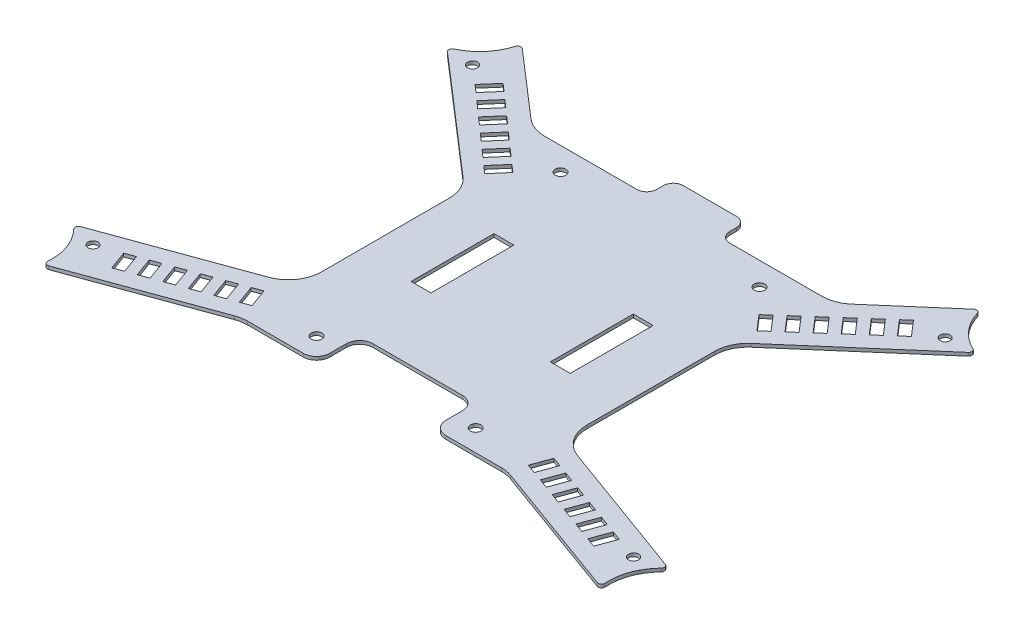
SolidWorks part; units mm, degrees
material "Thornel Mat VMA"
ref_plane "Front Plane" through (0, 0, 0) normal (0, 0, 1) x (1, 0, 0)
ref_plane "Top Plane" through (0, 0, 0) normal (0, 1, 0) x (1, 0, 0)
ref_plane "Right Plane" through (0, 0, 0) normal (1, 0, 0) x (0, 0, -1)
sketch "Sketch2" plane through (0, 0, 0) normal (0, 1, 0) x (1, 0, 0)
  line L24 (11, 53) -> (11, 55)
  line L25 (8, 58) -> (-8, 58)
  line L26 (-11, 55) -> (-11, 53)
  line L27 (-14, 50) -> (-41.7933, 50)
  line L28 (-48.3393, 52.4403) -> (-69.5576, 70.8135)
  line L29 (-80.0313, 58.718) -> (-43.4539, 27.0451)
  line L30 (-40, 19.4854) -> (-40, -19.0433)
  line L31 (-46.5798, -28.4402) -> (-90.0503, -44.2622)
  line L32 (-84.578, -59.2973) -> (-41.6569, -43.6753)
  line L33 (-38.2367, -43.0722) -> (-21.5, -43.0722)
  line L34 (-17.5, -39.0722) -> (-17.5, -34.0722)
  line L35 (-13.5, -30.0722) -> (13.5, -30.0722)
  line L36 (17.5, -34.0722) -> (17.5, -39.0722)
  line L37 (21.5, -43.0722) -> (38.2367, -43.0722)
  line L38 (41.6569, -43.6753) -> (84.578, -59.2973)
  line L39 (90.0503, -44.2622) -> (46.5798, -28.4402)
  line L40 (40, -19.0433) -> (40, 19.4854)
  line L41 (43.4539, 27.0451) -> (80.0313, 58.718)
  line L42 (69.5576, 70.8135) -> (48.3393, 52.4403)
  line L43 (41.7933, 50) -> (14, 50)
  line L88 (-48.3393, 52.4403) -> (-68.0517, 69.5096)
  line L89 (-78.5254, 57.4141) -> (-43.4539, 27.0451)
  line L90 (-40, 19.4854) -> (-40, -19.0433)
  line L91 (-46.5798, -28.4402) -> (-88.1785, -43.5809)
  line L92 (-82.7062, -58.616) -> (-41.6569, -43.6753)
  line L93 (-38.2367, -43.0722) -> (-21.5, -43.0722)
  line L94 (-17.5, -39.0722) -> (-17.5, -34.0722)
  line L95 (-13.5, -30.0722) -> (13.5, -30.0722)
  line L96 (17.5, -34.0722) -> (17.5, -39.0722)
  line L97 (21.5, -43.0722) -> (38.2367, -43.0722)
  line L98 (41.6569, -43.6753) -> (82.7062, -58.616)
  line L99 (88.1785, -43.5809) -> (46.5798, -28.4402)
  line L100 (40, -19.0433) -> (40, 19.4854)
  line L101 (43.4539, 27.0451) -> (78.5254, 57.4141)
  line L102 (68.0517, 69.5096) -> (48.3393, 52.4403)
  line L103 (41.7933, 50) -> (14, 50)
  line L104 (11, 53) -> (11, 55)
  line L105 (8, 58) -> (-8, 58)
  line L106 (11, 53) -> (11, 55)
  line L107 (-14, 50) -> (-41.7933, 50)
  line L108 (-48.3393, 52.4403) -> (-68.0517, 69.5096)
  line L109 (-78.5254, 57.4141) -> (-43.4539, 27.0451)
  line L110 (-40, 19.4854) -> (-40, -19.0433)
  line L111 (-46.5798, -28.4402) -> (-88.1785, -43.5809)
  line L112 (-82.7062, -58.616) -> (-41.6569, -43.6753)
  line L113 (-38.2367, -43.0722) -> (-21.5, -43.0722)
  line L114 (-17.5, -39.0722) -> (-17.5, -34.0722)
  line L115 (-13.5, -30.0722) -> (13.5, -30.0722)
  line L116 (17.5, -34.0722) -> (17.5, -39.0722)
  line L117 (21.5, -43.0722) -> (38.2367, -43.0722)
  line L118 (41.6569, -43.6753) -> (82.7062, -58.616)
  line L119 (88.1785, -43.5809) -> (46.5798, -28.4402)
  line L120 (40, -19.0433) -> (40, 19.4854)
  line L121 (43.4539, 27.0451) -> (78.5254, 57.4141)
  line L122 (68.0517, 69.5096) -> (48.3393, 52.4403)
  line L123 (41.7933, 50) -> (14, 50)
  line L125 (8, 58) -> (-8, 58)
  line L127 (-14, 50) -> (-41.7933, 50)
  line L180 (-11, 55) -> (-11, 53)
  line L181 (-11, 55) -> (-11, 53)
  arc A28 (11, 55) -> (8, 58) centre (8, 55) ccw
  arc A29 (-8, 58) -> (-11, 55) centre (-8, 55) ccw
  arc A30 (-14, 50) -> (-11, 53) centre (-14, 53) ccw
  arc A31 (-48.3393, 52.4403) -> (-41.7933, 50) centre (-41.7933, 60) ccw
  arc A32 (-72.7842, 76.2531) -> (-69.5576, 70.8135) centre (-63.0115, 78.3732) ccw
  arc A33 (-72.7842, 76.2531) -> (-85.8763, 61.1337) centre (-85, 73.603) ccw
  arc A34 (-80.0313, 58.718) -> (-85.8763, 61.1337) centre (-86.5773, 51.1583) ccw
  arc A35 (-40, 19.4854) -> (-43.4539, 27.0451) centre (-50, 19.4854) ccw
  arc A36 (-46.5798, -28.4402) -> (-40, -19.0433) centre (-50, -19.0433) ccw
  arc A37 (-96.3725, -44.4349) -> (-90.0503, -44.2622) centre (-93.4705, -34.8653) ccw
  arc A38 (-96.3725, -44.4349) -> (-89.5321, -63.2288) centre (-100, -56.397) ccw
  arc A39 (-84.578, -59.2973) -> (-89.5321, -63.2288) centre (-81.1578, -68.6942) ccw
  arc A40 (-38.2367, -43.0722) -> (-41.6569, -43.6753) centre (-38.2367, -53.0722) ccw
  arc A41 (-21.5, -43.0722) -> (-17.5, -39.0722) centre (-21.5, -39.0722) ccw
  arc A42 (-13.5, -30.0722) -> (-17.5, -34.0722) centre (-13.5, -34.0722) ccw
  arc A43 (17.5, -34.0722) -> (13.5, -30.0722) centre (13.5, -34.0722) ccw
  arc A44 (17.5, -39.0722) -> (21.5, -43.0722) centre (21.5, -39.0722) ccw
  arc A45 (41.6569, -43.6753) -> (38.2367, -43.0722) centre (38.2367, -53.0722) ccw
  arc A46 (89.5321, -63.2288) -> (84.578, -59.2973) centre (81.1578, -68.6942) ccw
  arc A47 (89.5321, -63.2288) -> (96.3725, -44.4349) centre (100, -56.397) ccw
  arc A48 (90.0503, -44.2622) -> (96.3725, -44.4349) centre (93.4705, -34.8653) ccw
  arc A49 (40, -19.0433) -> (46.5798, -28.4402) centre (50, -19.0433) ccw
  arc A50 (43.4539, 27.0451) -> (40, 19.4854) centre (50, 19.4854) ccw
  arc A51 (85.8763, 61.1337) -> (80.0313, 58.718) centre (86.5773, 51.1583) ccw
  arc A52 (85.8763, 61.1337) -> (72.7842, 76.2531) centre (85, 73.603) ccw
  arc A53 (69.5576, 70.8135) -> (72.7842, 76.2531) centre (63.0115, 78.3732) ccw
  arc A54 (41.7933, 50) -> (48.3393, 52.4403) centre (41.7933, 60) ccw
  arc A55 (11, 53) -> (14, 50) centre (14, 53) ccw
  arc A61 (-72.7842, 76.2531) -> (-85.8763, 61.1337) centre (-85, 73.603) ccw construction
  arc A80 (85.8763, 61.1337) -> (72.7842, 76.2531) centre (85, 73.603) ccw construction
  arc A81 (69.5576, 70.8135) -> (72.7842, 76.2531) centre (63.0115, 78.3732) ccw construction
  arc A113 (-78.2902, 59.0779) -> (-69.6648, 69.0389) centre (-85, 73.603) ccw
  arc A115 (-40, 19.4854) -> (-43.4539, 27.0451) centre (-50, 19.4854) ccw
  arc A116 (-46.5798, -28.4402) -> (-40, -19.0433) centre (-50, -19.0433) ccw
  arc A118 (-84.0454, -57.6011) -> (-88.552, -45.2192) centre (-100, -56.397) ccw
  arc A120 (-38.2367, -43.0722) -> (-41.6569, -43.6753) centre (-38.2367, -53.0722) ccw
  arc A121 (-21.5, -43.0722) -> (-17.5, -39.0722) centre (-21.5, -39.0722) ccw
  arc A122 (-13.5, -30.0722) -> (-17.5, -34.0722) centre (-13.5, -34.0722) ccw
  arc A123 (17.5, -34.0722) -> (13.5, -30.0722) centre (13.5, -34.0722) ccw
  arc A124 (17.5, -39.0722) -> (21.5, -43.0722) centre (21.5, -39.0722) ccw
  arc A125 (41.6569, -43.6753) -> (38.2367, -43.0722) centre (38.2367, -53.0722) ccw
  arc A127 (88.552, -45.2192) -> (84.0454, -57.6011) centre (100, -56.397) ccw
  arc A129 (40, -19.0433) -> (46.5798, -28.4402) centre (50, -19.0433) ccw
  arc A130 (43.4539, 27.0451) -> (40, 19.4854) centre (50, 19.4854) ccw
  arc A132 (69.6648, 69.0389) -> (78.2902, 59.0779) centre (85, 73.603) ccw
  arc A134 (41.7933, 50) -> (48.3393, 52.4403) centre (41.7933, 60) ccw
  arc A135 (11, 53) -> (14, 50) centre (14, 53) ccw
  arc A136 (11, 55) -> (8, 58) centre (8, 55) ccw
  arc A137 (-8, 58) -> (-11, 55) centre (-8, 55) ccw
  arc A138 (-14, 50) -> (-11, 53) centre (-14, 53) ccw
  arc A139 (-48.3393, 52.4403) -> (-41.7933, 50) centre (-41.7933, 60) ccw
  arc A141 (-78.2902, 59.0779) -> (-69.6648, 69.0389) centre (-85, 73.603) ccw
  arc A143 (-40, 19.4854) -> (-43.4539, 27.0451) centre (-50, 19.4854) ccw
  arc A144 (-46.5798, -28.4402) -> (-40, -19.0433) centre (-50, -19.0433) ccw
  arc A146 (-84.0454, -57.6011) -> (-88.552, -45.2192) centre (-100, -56.397) ccw
  arc A148 (-38.2367, -43.0722) -> (-41.6569, -43.6753) centre (-38.2367, -53.0722) ccw
  arc A149 (-21.5, -43.0722) -> (-17.5, -39.0722) centre (-21.5, -39.0722) ccw
  arc A150 (-13.5, -30.0722) -> (-17.5, -34.0722) centre (-13.5, -34.0722) ccw
  arc A151 (17.5, -34.0722) -> (13.5, -30.0722) centre (13.5, -34.0722) ccw
  arc A152 (17.5, -39.0722) -> (21.5, -43.0722) centre (21.5, -39.0722) ccw
  arc A153 (41.6569, -43.6753) -> (38.2367, -43.0722) centre (38.2367, -53.0722) ccw
  arc A155 (88.552, -45.2192) -> (84.0454, -57.6011) centre (100, -56.397) ccw
  arc A157 (40, -19.0433) -> (46.5798, -28.4402) centre (50, -19.0433) ccw
  arc A158 (43.4539, 27.0451) -> (40, 19.4854) centre (50, 19.4854) ccw
  arc A160 (69.6648, 69.0389) -> (78.2902, 59.0779) centre (85, 73.603) ccw
  arc A162 (41.7933, 50) -> (48.3393, 52.4403) centre (41.7933, 60) ccw
  arc A163 (11, 53) -> (14, 50) centre (14, 53) ccw
  arc A164 (11, 55) -> (8, 58) centre (8, 55) ccw
  arc A165 (-8, 58) -> (-11, 55) centre (-8, 55) ccw
  arc A166 (-14, 50) -> (-11, 53) centre (-14, 53) ccw
  arc A167 (-48.3393, 52.4403) -> (-41.7933, 50) centre (-41.7933, 60) ccw
  spline S16 degree 3 poles (-68.0517, 69.5096) (-68.6611, 70.0373) (-69.4348, 69.8115) (-69.6648, 69.0389) knots 0 0 0 0 1 1 1 1 weights 1 0.694884 0.694884 1
  spline S17 degree 3 poles (-68.0517, 69.5096) (-68.6611, 70.0373) (-69.4348, 69.8115) (-69.6648, 69.0389) knots 0 0 0 0 1 1 1 1 weights 1 0.694884 0.694884 1
  spline S18 degree 3 poles (-78.2902, 59.0779) (-79.0219, 58.7399) (-79.1348, 57.9417) (-78.5254, 57.4141) knots 0 0 0 0 1 1 1 1 weights 1 0.694884 0.694884 1
  spline S19 degree 3 poles (-78.2902, 59.0779) (-79.0219, 58.7399) (-79.1348, 57.9417) (-78.5254, 57.4141) knots 0 0 0 0 1 1 1 1 weights 1 0.694884 0.694884 1
  spline S20 degree 3 poles (-88.1785, -43.5809) (-88.9359, -43.8566) (-89.1151, -44.6425) (-88.552, -45.2192) knots 0 0 0 0 1 1 1 1 weights 1 0.694884 0.694884 1
  spline S21 degree 3 poles (-88.1785, -43.5809) (-88.9359, -43.8566) (-89.1151, -44.6425) (-88.552, -45.2192) knots 0 0 0 0 1 1 1 1 weights 1 0.694884 0.694884 1
  spline S22 degree 3 poles (-84.0454, -57.6011) (-84.106, -58.4048) (-83.4636, -58.8917) (-82.7062, -58.616) knots 0 0 0 0 1 1 1 1 weights 1 0.694884 0.694884 1
  spline S23 degree 3 poles (-84.0454, -57.6011) (-84.106, -58.4048) (-83.4636, -58.8917) (-82.7062, -58.616) knots 0 0 0 0 1 1 1 1 weights 1 0.694884 0.694884 1
  spline S24 degree 3 poles (82.7062, -58.616) (83.4636, -58.8917) (84.106, -58.4048) (84.0454, -57.6011) knots 0 0 0 0 1 1 1 1 weights 1 0.694884 0.694884 1
  spline S25 degree 3 poles (82.7062, -58.616) (83.4636, -58.8917) (84.106, -58.4048) (84.0454, -57.6011) knots 0 0 0 0 1 1 1 1 weights 1 0.694884 0.694884 1
  spline S26 degree 3 poles (88.552, -45.2192) (89.1151, -44.6425) (88.9359, -43.8566) (88.1785, -43.5809) knots 0 0 0 0 1 1 1 1 weights 1 0.694884 0.694884 1
  spline S27 degree 3 poles (88.552, -45.2192) (89.1151, -44.6425) (88.9359, -43.8566) (88.1785, -43.5809) knots 0 0 0 0 1 1 1 1 weights 1 0.694884 0.694884 1
  spline S28 degree 3 poles (78.5254, 57.4141) (79.1348, 57.9417) (79.0219, 58.7399) (78.2902, 59.0779) knots 0 0 0 0 1 1 1 1 weights 1 0.694884 0.694884 1
  spline S29 degree 3 poles (78.5254, 57.4141) (79.1348, 57.9417) (79.0219, 58.7399) (78.2902, 59.0779) knots 0 0 0 0 1 1 1 1 weights 1 0.694884 0.694884 1
  spline S30 degree 3 poles (69.6648, 69.0389) (69.4348, 69.8115) (68.6611, 70.0373) (68.0517, 69.5096) knots 0 0 0 0 1 1 1 1 weights 1 0.694884 0.694884 1
  spline S31 degree 3 poles (69.6648, 69.0389) (69.4348, 69.8115) (68.6611, 70.0373) (68.0517, 69.5096) knots 0 0 0 0 1 1 1 1 weights 1 0.694884 0.694884 1
  dimension "D1" = 0
  dimension "D2" = 0
extrude "Boss-Extrude1" add sketch "Sketch2" along normal blind 1
sketch "Sketch5" plane through (0, 1, 0) normal (0, 1, 0) x (1, 0, 0)
  circle A0 centre (24, -36.5722) radius 1.6 construction
  circle A1 centre (24, -36.5722) radius 1.6
  circle A2 centre (-24, -36.5722) radius 1.6 construction
  circle A3 centre (-24, -36.5722) radius 1.6
  circle A4 centre (-30, 43) radius 1.6 construction
  circle A5 centre (-30, 43) radius 1.6
  circle A6 centre (30, 43) radius 1.6 construction
  circle A7 centre (30, 43) radius 1.6
extrude "Cut-Extrude1" cut sketch "Sketch5" against normal through all
sketch "Sketch6" plane through (0, 1, 0) normal (0, 1, 0) x (1, 0, 0)
  line L0 (0, 0) -> (0, -50000) construction
  line L1 (-38.2367, -43.0722) -> (-21.5, -43.0722) construction
  line L7 (-24, 16.9278) -> (-18, 16.9278)
  line L8 (-24, 16.9278) -> (-24, -8.0722)
  line L9 (-24, -8.0722) -> (-18, -8.0722)
  line L10 (-18, 16.9278) -> (-18, -8.0722)
  line L11 (18, 16.9278) -> (18, -8.0722)
  line L12 (24, -8.0722) -> (18, -8.0722)
  line L13 (24, 16.9278) -> (24, -8.0722)
  line L14 (24, 16.9278) -> (18, 16.9278)
  dimension "D1" = 6
  dimension "D2" = 18
  dimension "D3" = 25
  dimension "D4" = 35
extrude "Cut-Extrude2" cut sketch "Sketch6" against normal through all
sketch "Sketch7" plane through (0, 1, 0) normal (0, 1, 0) x (1, 0, 0)
  line L0 (-65.7967, 53.0061) -> (-61.869, 57.5419)
  line L1 (-61.869, 57.5419) -> (-59.6011, 55.5781)
  line L2 (-59.6011, 55.5781) -> (-63.5288, 51.0423)
  line L3 (-63.5288, 51.0423) -> (-65.7967, 53.0061)
  line L4 (-78.5254, 57.4141) -> (-43.4539, 27.0451) construction
  line L5 (-61.2977, 49.0364) -> (-57.3701, 53.5722)
  line L6 (-57.3701, 53.5722) -> (-55.1022, 51.6084)
  line L7 (-55.1022, 51.6084) -> (-59.0298, 47.0726)
  line L8 (-59.0298, 47.0726) -> (-61.2977, 49.0364)
  line L9 (-56.7988, 45.0667) -> (-52.8711, 49.6026)
  line L10 (-52.8711, 49.6026) -> (-50.6032, 47.6387)
  line L11 (-50.6032, 47.6387) -> (-54.5309, 43.1029)
  line L12 (-54.5309, 43.1029) -> (-56.7988, 45.0667)
  line L13 (-52.2998, 41.0971) -> (-48.3722, 45.6329)
  line L14 (-48.3722, 45.6329) -> (-46.1043, 43.6691)
  line L15 (-46.1043, 43.6691) -> (-50.0319, 39.1333)
  line L16 (-50.0319, 39.1333) -> (-52.2998, 41.0971)
  line L17 (-47.8009, 37.1274) -> (-43.8732, 41.6632)
  line L18 (-43.8732, 41.6632) -> (-41.6053, 39.6994)
  line L19 (-41.6053, 39.6994) -> (-45.533, 35.1636)
  line L20 (-45.533, 35.1636) -> (-47.8009, 37.1274)
  line L21 (-43.3019, 33.1578) -> (-39.3743, 37.6936)
  line L22 (-39.3743, 37.6936) -> (-37.1064, 35.7298)
  line L23 (-37.1064, 35.7298) -> (-41.034, 31.1939)
  line L24 (-41.034, 31.1939) -> (-43.3019, 33.1578)
  line L25 (0, 0) -> (0, -50000) construction
  line L26 (41.034, 31.1939) -> (43.3019, 33.1578)
  line L27 (37.1064, 35.7298) -> (41.034, 31.1939)
  line L28 (39.3743, 37.6936) -> (37.1064, 35.7298)
  line L29 (43.3019, 33.1578) -> (39.3743, 37.6936)
  line L30 (45.533, 35.1636) -> (47.8009, 37.1274)
  line L31 (41.6053, 39.6994) -> (45.533, 35.1636)
  line L32 (43.8732, 41.6632) -> (41.6053, 39.6994)
  line L33 (47.8009, 37.1274) -> (43.8732, 41.6632)
  line L34 (50.0319, 39.1333) -> (52.2998, 41.0971)
  line L35 (46.1043, 43.6691) -> (50.0319, 39.1333)
  line L36 (48.3722, 45.6329) -> (46.1043, 43.6691)
  line L37 (52.2998, 41.0971) -> (48.3722, 45.6329)
  line L38 (54.5309, 43.1029) -> (56.7988, 45.0667)
  line L39 (50.6032, 47.6387) -> (54.5309, 43.1029)
  line L40 (52.8711, 49.6026) -> (50.6032, 47.6387)
  line L41 (56.7988, 45.0667) -> (52.8711, 49.6026)
  line L42 (59.0298, 47.0726) -> (61.2977, 49.0364)
  line L43 (55.1022, 51.6084) -> (59.0298, 47.0726)
  line L44 (57.3701, 53.5722) -> (55.1022, 51.6084)
  line L45 (61.2977, 49.0364) -> (57.3701, 53.5722)
  line L46 (63.5288, 51.0423) -> (65.7967, 53.0061)
  line L47 (59.6011, 55.5781) -> (63.5288, 51.0423)
  line L48 (61.869, 57.5419) -> (59.6011, 55.5781)
  line L49 (65.7967, 53.0061) -> (61.869, 57.5419)
  line L50 (-74.7147, -44.0014) -> (-72.6625, -49.6395)
  line L51 (-72.6625, -49.6395) -> (-69.8435, -48.6135)
  line L52 (-69.8435, -48.6135) -> (-71.8956, -42.9753)
  line L53 (-71.8956, -42.9753) -> (-74.7147, -44.0014)
  line L54 (-82.7062, -58.616) -> (-41.6569, -43.6753) construction
  line L99 (-69.0765, -41.9493) -> (-67.0244, -47.5874)
  line L100 (-46.5798, -28.4402) -> (-88.1785, -43.5809) construction
  line L101 (-67.0244, -47.5874) -> (-64.2053, -46.5614)
  line L102 (-64.2053, -46.5614) -> (-66.2574, -40.9232)
  line L103 (-66.2574, -40.9232) -> (-69.0765, -41.9493)
  line L104 (-63.4384, -39.8971) -> (-61.3862, -45.5353)
  line L105 (-61.3862, -45.5353) -> (-58.5672, -44.5092)
  line L106 (-58.5672, -44.5092) -> (-60.6193, -38.8711)
  line L107 (-60.6193, -38.8711) -> (-63.4384, -39.8971)
  line L108 (-57.8002, -37.845) -> (-55.7481, -43.4832)
  line L109 (-55.7481, -43.4832) -> (-52.929, -42.4571)
  line L110 (-52.929, -42.4571) -> (-54.9811, -36.819)
  line L111 (-54.9811, -36.819) -> (-57.8002, -37.845)
  line L112 (-52.162, -35.7929) -> (-50.1099, -41.4311)
  line L113 (-50.1099, -41.4311) -> (-47.2908, -40.405)
  line L114 (-47.2908, -40.405) -> (-49.343, -34.7668)
  line L115 (-49.343, -34.7668) -> (-52.162, -35.7929)
  line L116 (-46.5239, -33.7408) -> (-44.4718, -39.3789)
  line L117 (-44.4718, -39.3789) -> (-41.6527, -38.3529)
  line L118 (-41.6527, -38.3529) -> (-43.7048, -32.7147)
  line L119 (-43.7048, -32.7147) -> (-46.5239, -33.7408)
  line L120 (43.7048, -32.7147) -> (46.5239, -33.7408)
  line L121 (41.6527, -38.3529) -> (43.7048, -32.7147)
  line L122 (44.4718, -39.3789) -> (41.6527, -38.3529)
  line L123 (46.5239, -33.7408) -> (44.4718, -39.3789)
  line L124 (49.343, -34.7668) -> (52.162, -35.7929)
  line L125 (47.2908, -40.405) -> (49.343, -34.7668)
  line L126 (50.1099, -41.4311) -> (47.2908, -40.405)
  line L127 (52.162, -35.7929) -> (50.1099, -41.4311)
  line L128 (54.9811, -36.819) -> (57.8002, -37.845)
  line L129 (52.929, -42.4571) -> (54.9811, -36.819)
  line L130 (55.7481, -43.4832) -> (52.929, -42.4571)
  line L131 (57.8002, -37.845) -> (55.7481, -43.4832)
  line L132 (60.6193, -38.8711) -> (63.4384, -39.8971)
  line L133 (58.5672, -44.5092) -> (60.6193, -38.8711)
  line L134 (61.3862, -45.5353) -> (58.5672, -44.5092)
  line L135 (63.4384, -39.8971) -> (61.3862, -45.5353)
  line L136 (66.2574, -40.9232) -> (69.0765, -41.9493)
  line L137 (64.2053, -46.5614) -> (66.2574, -40.9232)
  line L138 (67.0244, -47.5874) -> (64.2053, -46.5614)
  line L139 (69.0765, -41.9493) -> (67.0244, -47.5874)
  line L140 (71.8956, -42.9753) -> (74.7147, -44.0014)
  line L141 (69.8435, -48.6135) -> (71.8956, -42.9753)
  line L142 (72.6625, -49.6395) -> (69.8435, -48.6135)
  line L143 (74.7147, -44.0014) -> (72.6625, -49.6395)
  arc A0 (-78.2902, 59.0779) -> (-69.6648, 69.0389) centre (-85, 73.603) ccw construction
  arc A1 (-84.0454, -57.6011) -> (-88.552, -45.2192) centre (-100, -56.397) ccw construction
  dimension "D1" = 6
  dimension "D2" = 3
  dimension "D3" = 5
  dimension "D5" = 5.9996
  dimension "D6" = 28
  dimension "D7" = 28
  dimension "D9" = 5
  dimension "D10" = 6
  dimension "D4" = 6
  dimension "D8" = 6
extrude "Cut-Extrude3" cut sketch "Sketch7" against normal through all
sketch "Sketch8" plane through (0, 1, 0) normal (0, 1, 0) x (1, 0, 0)
  line L1 (0, 0) -> (0, -50000) construction
  circle A5 centre (-81.4949, -46.4692) radius 1.5
  circle A6 centre (-81.4949, -46.4692) radius 1.5
  circle A7 centre (-71.2513, 57.7293) radius 1.5
  circle A8 centre (-71.2513, 57.7293) radius 1.5
  circle A9 centre (71.2513, 57.7293) radius 1.5
  circle A10 centre (71.2513, 57.7293) radius 1.5
  circle A11 centre (81.4949, -46.4692) radius 1.5
  circle A12 centre (81.4949, -46.4692) radius 1.5
  dimension "D1" = 0
  dimension "D2" = 0
  dimension "D3" = 0
  dimension "D4" = 0
extrude "Cut-Extrude4" cut sketch "Sketch8" against normal through all
